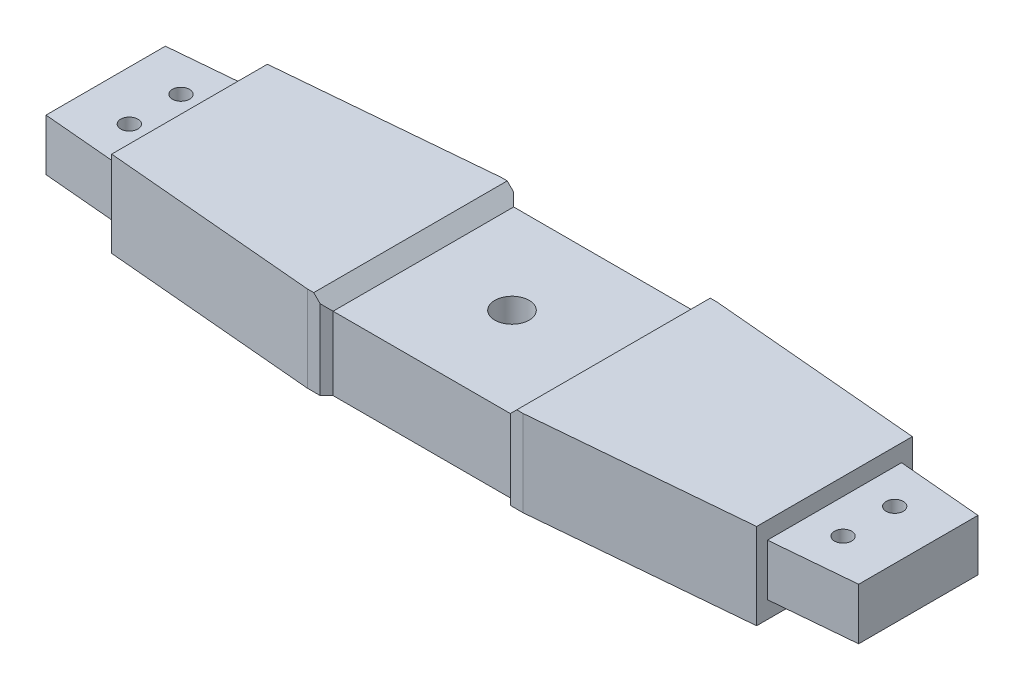
SolidWorks part; units mm, degrees
ref_plane "Front" through (0, 0, 0) normal (0, 0, 1) x (1, 0, 0)
ref_plane "Top" through (0, 0, 0) normal (0, 1, 0) x (1, 0, 0)
ref_plane "Right" through (0, 0, 0) normal (1, 0, 0) x (0, 0, -1)
sketch "Sketch1" plane through (0, 0, 0) normal (0, 1, 0) x (1, 0, 0)
  line L0 (0, 0) -> (0, 20) construction
  line L1 (-25, 20) -> (25, 20)
  line L2 (-161.6019, 7.9692) -> (-25, 20)
  line L3 (25, 20) -> (161.6019, 7.9692)
  line L4 (-160.9, 0) -> (160.9, 0) construction
  line L5 (-161.6019, -7.9692) -> (-25, -20)
  line L6 (-25, -20) -> (25, -20)
  line L7 (25, -20) -> (161.6019, -7.9692)
  line L9 (-95, -25) -> (95, -25)
  line L10 (-95, -25) -> (-95, 25)
  line L11 (-95, 25) -> (95, 25)
  line L12 (95, -25) -> (95, 25)
  line L13 (-95, -25) -> (95, 25) construction
  line L14 (-95, 25) -> (95, -25) construction
  circle A0 centre (0, 0) radius 4
  circle A1 centre (-160.9, 0) radius 4
  circle A2 centre (160.9, 0) radius 4
  circle A3 centre (160.9, 0) radius 8
  circle A4 centre (-160.9, 0) radius 8
  dimension "D1" = 8
  dimension "D2" = 8
  dimension "D3" = 8
  dimension "D6" = 160.9
  dimension "D7" = 160.9
  dimension "D8" = 20
  dimension "D9" = 50
  dimension "D10" = 50
  dimension "D11" = 190
  dimension "D4" = 4
  dimension "D5" = 4
extrude "Boss-Extrude1" add sketch "Sketch1" along normal blind 12 contours L7 L12 L3 L1 L2 L10 L5 L6 A0
sketch "Sketch2" plane through (0, 12, 0) normal (0, 1, 0) x (1, 0, 0)
  line L8 (-75, 18.1061) -> (-75, -18.1061)
  line L9 (-95, -13.8349) -> (-95, 13.8349) construction
  line L10 (75, 18.1061) -> (75, -18.1061)
  line L11 (95, -13.8349) -> (95, 13.8349) construction
  line L16 (25.1099, -22.5) -> (97.5, -16.1244)
  line L17 (97.5, -16.1244) -> (97.5, 16.1244)
  line L18 (97.5, 16.1244) -> (25.1099, 22.5)
  line L19 (25.1099, 22.5) -> (-25.1099, 22.5)
  line L20 (-25.1099, 22.5) -> (-97.5, 16.1244)
  line L21 (-97.5, 16.1244) -> (-97.5, -16.1244)
  line L22 (-97.5, -16.1244) -> (-25.1099, -22.5)
  line L23 (-25.1099, -22.5) -> (25.1099, -22.5)
  line L24 (25.1099, -22.5) -> (97.5, -16.1244)
  line L25 (97.5, -16.1244) -> (97.5, 16.1244)
  line L26 (97.5, 16.1244) -> (25.1099, 22.5)
  line L27 (25.1099, 22.5) -> (-25.1099, 22.5)
  line L28 (-25.1099, 22.5) -> (-97.5, 16.1244)
  line L29 (-97.5, 16.1244) -> (-97.5, -16.1244)
  line L30 (-97.5, -16.1244) -> (-25.1099, -22.5)
  line L31 (-25.1099, -22.5) -> (25.1099, -22.5)
  circle M11 centre (0, 0) radius 4
  line M12 (25, -20) -> (95, -13.8349)
  line M14 (95, 13.8349) -> (25, 20)
  line M15 (25, 20) -> (-25, 20)
  line M16 (-25, 20) -> (-95, 13.8349)
  line M18 (-95, -13.8349) -> (-25, -20)
  line M19 (-25, -20) -> (25, -20)
  dimension "D2" = 20
  dimension "D3" = 20
  dimension "D1" = 2.5
extrude "Boss-Extrude2" add sketch "Sketch2" along normal blind 4 and the other way blind 16 contours L10 L8 M14 M15 M16 M18 M19 M12 M11 | L30 L31 L24 L10 L8 M12 M19 M18 | L27 L28 L8 L10 L26 M16 M15 M14
sketch "Sketch3" plane through (0, 0, 22.5) normal (0, 0, 1) x (1, 0, 0)
  line L0 (-25.1099, 16) -> (25.1099, 16) construction
  line L1 (-25.1099, 16) -> (25.1099, 16)
  line L2 (23.6099, 16) -> (20.6099, 13)
  line L3 (20.6099, 13) -> (-20.6099, 13)
  line L4 (-20.6099, 13) -> (-23.6099, 16)
  dimension "D1" = 1.5
  dimension "D2" = 45
  dimension "D3" = 45
  dimension "D4" = 3
  dimension "D5" = 1.5
extrude "Cut-Extrude1" cut sketch "Sketch3" against normal through all and the other way through all contours L4 L3 L2 L1
sketch "Sketch6" plane through (0, 0, -22.5) normal (0, 0, -1) x (-1, 0, 0)
  line L1 (-25.1099, -4) -> (25.1099, -4) construction
  circle A0 centre (-10, 4.5) radius 2.05
  circle A1 centre (10, 4.5) radius 2.05
  dimension "D1" = 4.1
  dimension "D2" = 4.1
  dimension "D3" = 10
  dimension "D4" = 10
  dimension "D5" = 8.5
extrude "Cut-Extrude3" cut sketch "Sketch6" against normal blind 6.5
sketch "Sketch7" plane through (0, 0, 0) normal (0, -1, 0) x (1, 0, 0)
  line L0 (-75, -18.1061) -> (-75, 18.1061) construction
  line L1 (0, 0) -> (0, 22.5) construction
  line L2 (-25.1099, 22.5) -> (25.1099, 22.5) construction
  circle A0 centre (-83, -6) radius 2
  circle A1 centre (-83, 6) radius 2
  circle A2 centre (83, 6) radius 2
  circle A3 centre (83, -6) radius 2
  dimension "D1" = 4
  dimension "D2" = 4
  dimension "D3" = 8
  dimension "D4" = 6
  dimension "D5" = 6
extrude "Cut-Extrude4" cut sketch "Sketch7" against normal through all
sketch "Sketch8" plane through (0, -4, 0) normal (0, -1, 0) x (1, 0, 0)
  line L0 (-22.1099, -22.5) -> (-20.6099, -21)
  line L1 (25.1099, -22.5) -> (-25.1099, -22.5) construction
  line L2 (-20.6099, -21) -> (20.6099, -21)
  line L3 (20.6099, -21) -> (22.1099, -22.5)
  line L4 (0, 0) -> (4, 0) construction
  line L5 (-22.1099, -22.5) -> (22.1099, -22.5)
  line L6 (-22.1099, 22.5) -> (22.1099, 22.5)
  line L7 (20.6099, 21) -> (22.1099, 22.5)
  line L8 (-20.6099, 21) -> (20.6099, 21)
  line L9 (-22.1099, 22.5) -> (-20.6099, 21)
  circle A0 centre (0, 0) radius 4 construction
  dimension "D1" = 45
  dimension "D2" = 1.5
  dimension "D3" = 3
  dimension "D4" = 3
extrude "Cut-Extrude5" cut sketch "Sketch8" against normal through all and the other way through all
sketch "Sketch9" plane through (0, 12, 0) normal (0, 1, 0) x (1, 0, 0)
  line L0 (-94.5, 13.879) -> (-94.5, -13.879)
  line L1 (-95, 13.8349) -> (-75, 15.5964) construction
  line L2 (-95, -13.8349) -> (-75, -15.5964) construction
  line L3 (-95, -13.8349) -> (-95, 13.8349) construction
  line L4 (-94.5, 13.879) -> (-95, 13.8349)
  line L5 (-95, 13.8349) -> (-95, -13.8349)
  line L6 (-95, -13.8349) -> (-94.5, -13.879)
  line L7 (94.5, 13.879) -> (94.5, -13.879)
  line L8 (75, 15.5964) -> (95, 13.8349) construction
  line L9 (75, -15.5964) -> (95, -13.8349) construction
  line L10 (94.5, -13.879) -> (95, -13.8349)
  line L11 (95, -13.8349) -> (95, 13.8349)
  line L12 (95, 13.8349) -> (94.5, 13.879)
  dimension "D1" = 0.5
  dimension "D2" = 0.5
extrude "Cut-Extrude6" cut sketch "Sketch9" against normal through all
